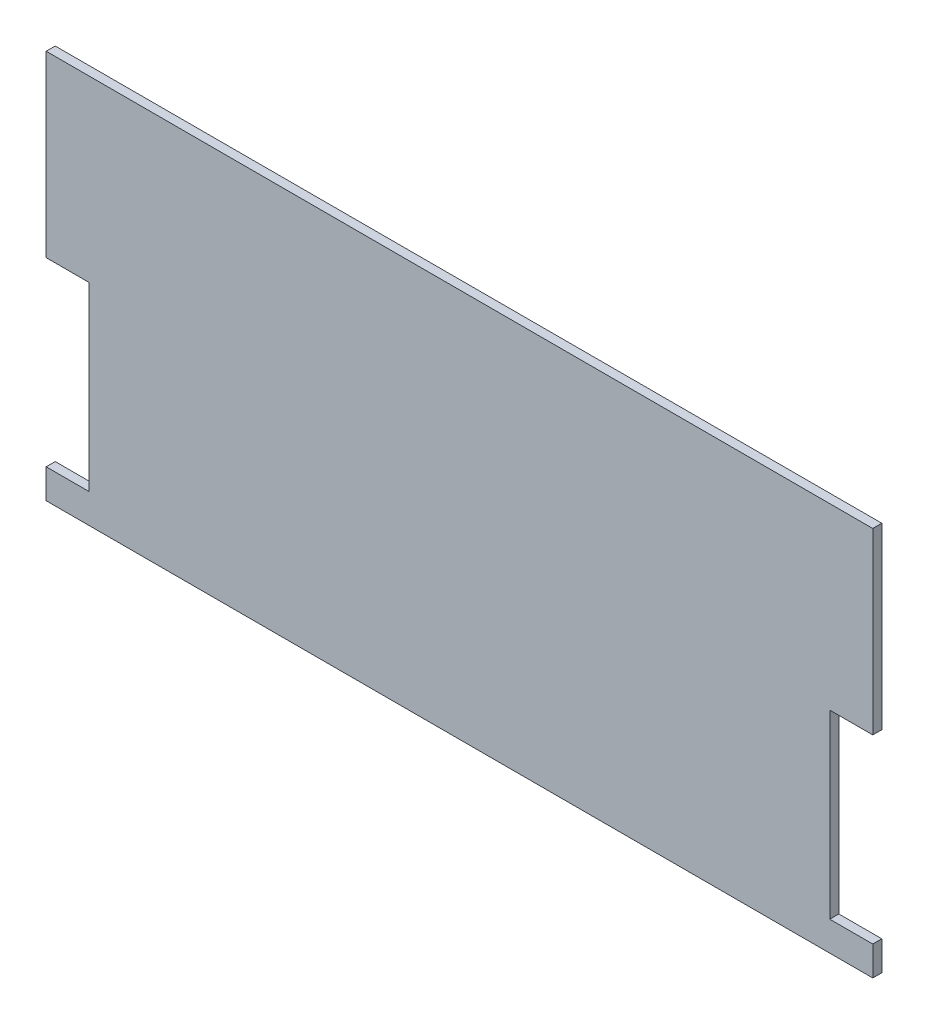
SolidWorks part; units mm, degrees
ref_plane "Ebene vorne" through (0, 0, 0) normal (0, 0, 1) x (1, 0, 0)
ref_plane "Ebene oben" through (0, 0, 0) normal (0, 1, 0) x (1, 0, 0)
ref_plane "Ebene rechts" through (0, 0, 0) normal (1, 0, 0) x (0, 0, -1)
sketch "Sketch1" plane through (0, 0, 0) normal (0, 0, 1) x (1, 0, 0)
  line L0 (0, -79.5) -> (0, -86)
  line L1 (0, 0) -> (182.6, 0)
  line L2 (0, 0) -> (0, -39.5)
  line L3 (0, -86) -> (182.6, -86)
  line L4 (182.6, 0) -> (182.6, -39.5)
  line L5 (0, -39.5) -> (9.5, -39.5)
  line L7 (0, -79.5) -> (9.5, -79.5)
  line L8 (9.5, -39.5) -> (9.5, -79.5)
  line L9 (182.6, -39.5) -> (173.1, -39.5)
  line L11 (182.6, -79.5) -> (173.1, -79.5)
  line L12 (173.1, -39.5) -> (173.1, -79.5)
  line L13 (182.6, -79.5) -> (182.6, -86)
  dimension "D1" = 182.6
  dimension "D2" = 86
  dimension "D3" = 40
  dimension "D4" = 40
  dimension "D5" = 39.5
  dimension "D6" = 39.5
  dimension "D7" = 9.5
  dimension "D8" = 9.5
extrude "Boss-Extrude1" add sketch "Sketch1" along normal blind 2
